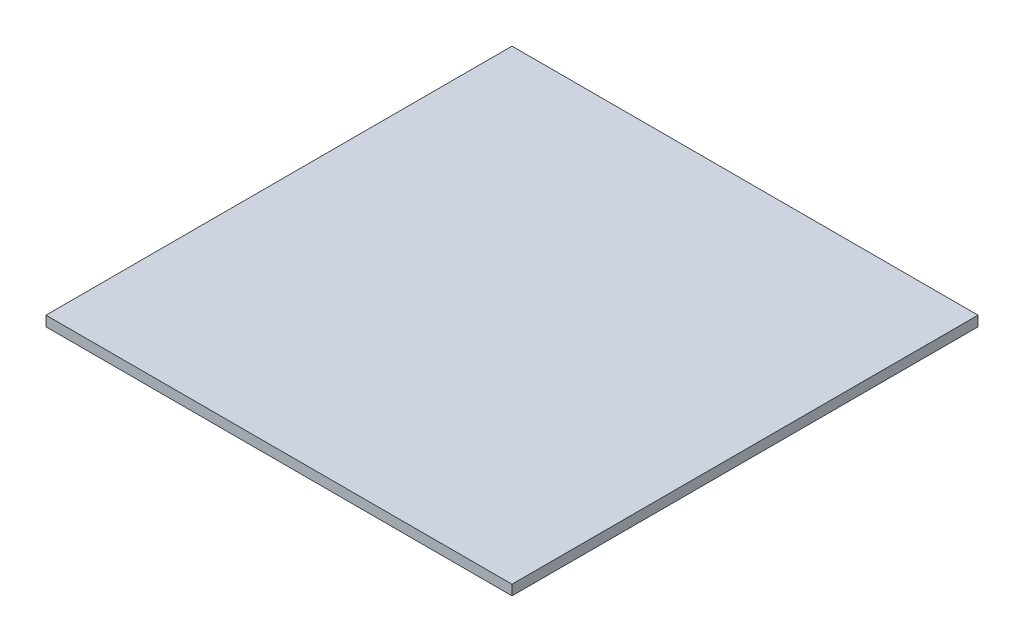
SolidWorks part; units mm, degrees
ref_plane "Front Plane" through (0, 0, 0) normal (0, 0, 1) x (1, 0, 0)
ref_plane "Top Plane" through (0, 0, 0) normal (0, 1, 0) x (1, 0, 0)
ref_plane "Right Plane" through (0, 0, 0) normal (1, 0, 0) x (0, 0, -1)
sketch "Sketch1" plane through (0, 0, 0) normal (0, 1, 0) x (1, 0, 0)
  line L1 (23, 23) -> (-23, 23)
  line L2 (23, 23) -> (23, -23)
  line L3 (23, -23) -> (-23, -23)
  line L4 (-23, 23) -> (-23, -23)
  line L5 (23, 23) -> (-23, -23) construction
  line L6 (23, -23) -> (-23, 23) construction
  point P0 (0, 0)
  dimension "D1" = 46
  dimension "D2" = 46
extrude "Boss-Extrude1" add sketch "Sketch1" along normal blind 1
